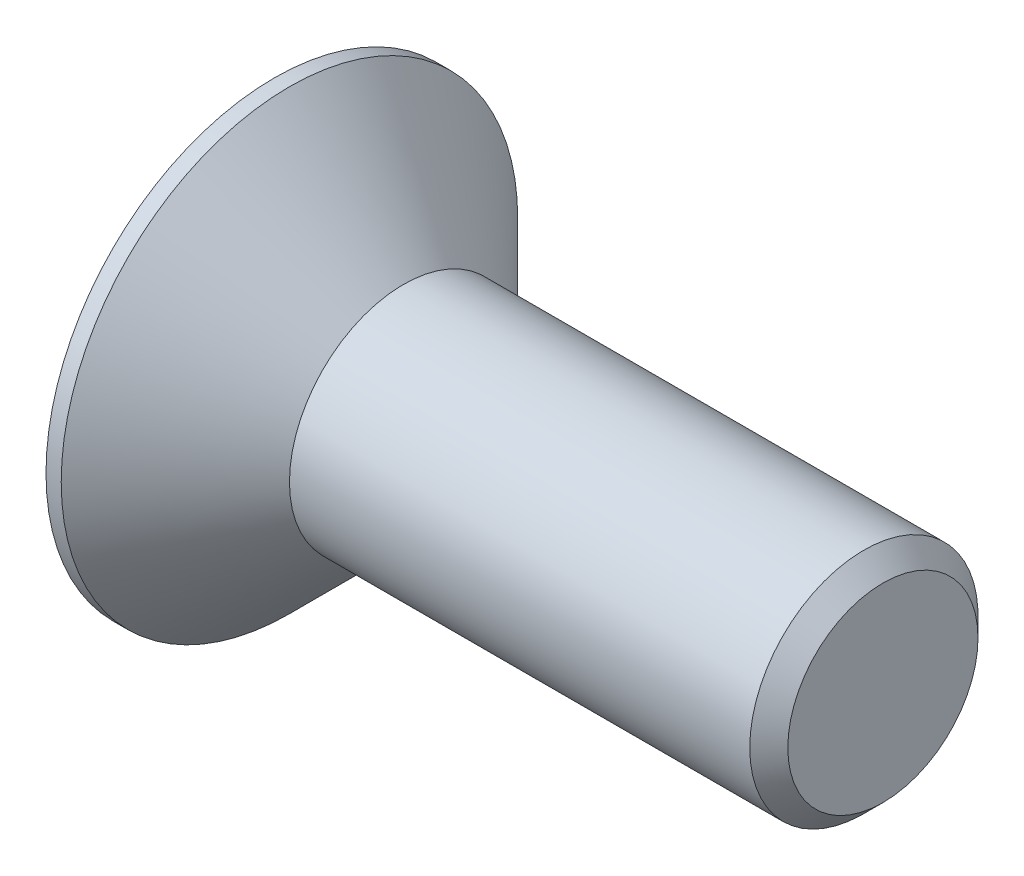
SolidWorks part; units mm, degrees
ref_plane "Front Plane" through (0, 0, 0) normal (0, 0, 1) x (1, 0, 0)
ref_plane "Top Plane" through (0, 0, 0) normal (0, 1, 0) x (1, 0, 0)
ref_plane "Right Plane" through (0, 0, 0) normal (1, 0, 0) x (0, 0, -1)
sketch "Sketch2" plane through (0, 0, 0) normal (0, 0, 1) x (1, 0, 0)
  line L0 (0, 0) -> (0, 3)
  line L1 (0, 3) -> (0.2, 3)
  line L2 (0.2, 3) -> (1.7, 1.5)
  line L3 (1.7, 1.5) -> (7.75, 1.5)
  line L4 (7.75, 1.5) -> (8, 1.25)
  line L5 (8, 1.25) -> (8, 0)
  line L6 (8, 0) -> (0, 0)
  line L7 (-2.2818, 0) -> (8.0811, 0) construction
  dimension "D1" = 6
  dimension "D2" = 0.2
  dimension "D3" = 45
  dimension "D4" = 8
  dimension "D5" = 0.25
  dimension "D6" = 3
revolve "Revolve1" add sketch "Sketch2" angle 360 about L7
sketch "Sketch3" plane through (0, 0, 0) normal (-1, 0, 0) x (0, 0, 1)
  line L1 (0.7217, -1.25) -> (1.4434, 0)
  line L2 (1.4434, 0) -> (0.7217, 1.25)
  line L3 (0.7217, 1.25) -> (-0.7217, 1.25)
  line L4 (-0.7217, 1.25) -> (-1.4434, 0)
  line L5 (-1.4434, 0) -> (-0.7217, -1.25)
  line L6 (-0.7217, -1.25) -> (0.7217, -1.25)
  circle A0 centre (0, 0) radius 1.25 construction
  dimension "D1" = 2.5
extrude "Cut-Extrude1" cut sketch "Sketch3" against normal blind 0.8
